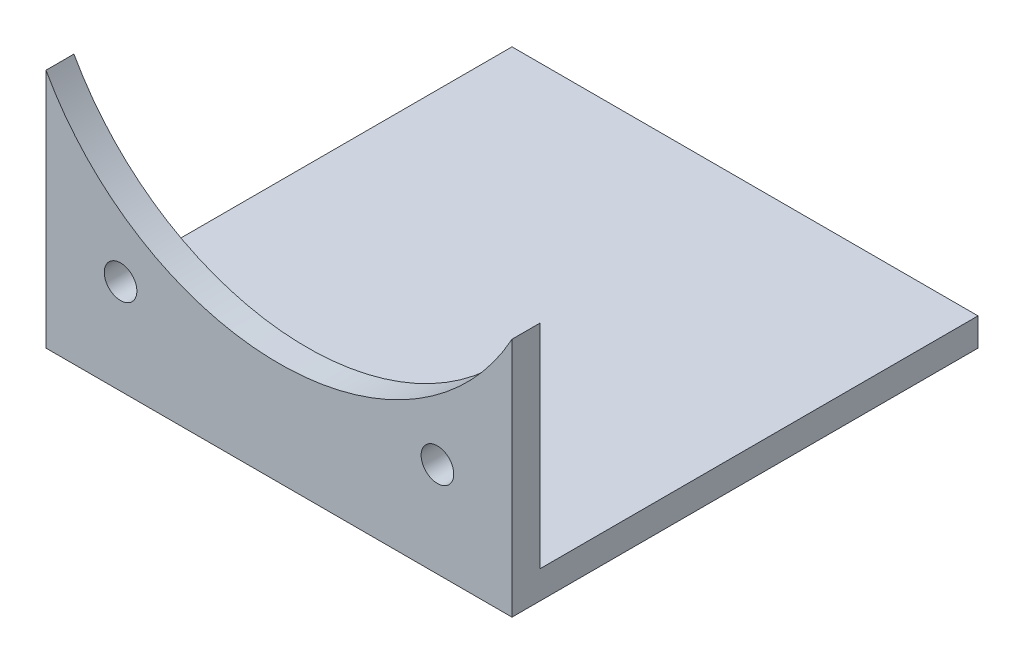
SolidWorks part; units mm, degrees
material "1060 合金"
ref_plane "前基準面" through (0, 0, 0) normal (0, 0, 1) x (1, 0, 0)
ref_plane "上基準面" through (0, 0, 0) normal (0, 1, 0) x (1, 0, 0)
ref_plane "右基準面" through (0, 0, 0) normal (1, 0, 0) x (0, 0, -1)
sketch "草圖1" plane through (0, 0, 0) normal (1, 0, 0) x (0, 0, -1)
  line L1 (0, 0) -> (3, 0)
  line L2 (0, 0) -> (0, 50)
  line L3 (0, 50) -> (3, 50)
  line L4 (3, 0) -> (3, 50)
  line L5 (3, 0) -> (50, 0)
  line L6 (3, 0) -> (3, 3)
  line L7 (3, 3) -> (50, 3)
  line L8 (50, 0) -> (50, 3)
  dimension "D1" = 50
  dimension "D2" = 50
  dimension "D3" = 3
  dimension "D4" = 3
extrude "填料-伸長1" add sketch "草圖1" along normal mid plane 50 contours L4 L3 L2 L1 | L5 L8 L7 L6
sketch "草圖2" plane through (0, 0, -3) normal (0, 0, -1) x (-1, 0, 0)
  line L0 (0, 27.5) -> (0, -27.5) construction
  line L1 (0, 39.6174) -> (17, 10.1725) construction
  circle A0 centre (0, 39.6174) radius 34 construction
  circle A1 centre (17, 10.1725) radius 1.75
  circle A2 centre (-17, 10.1725) radius 1.75
  circle A3 centre (-34, 39.6174) radius 1.75
  circle A4 centre (-17, 69.0623) radius 1.75
  circle A5 centre (17, 69.0623) radius 1.75
  circle A6 centre (34, 39.6174) radius 1.75
  circle A7 centre (0, 39.6174) radius 28.55
  point P19 (0, 39.6174)
  dimension "D1" = 3.5
  dimension "D3" = 68
  dimension "D5" = 57.1
  dimension "D2" = 30
  dimension "D4" = 6
extrude "除料-伸長1" cut sketch "草圖2" against normal through all
